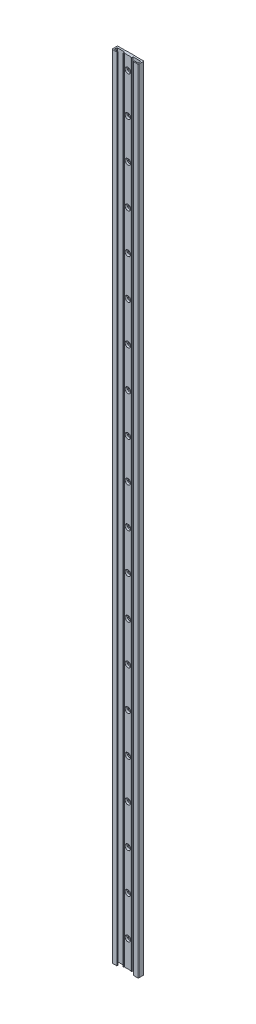
SolidWorks part; units mm, degrees
ref_plane "Front Plane" through (0, 0, 0) normal (0, 0, 1) x (1, 0, 0)
ref_plane "Top Plane" through (0, 0, 0) normal (0, 1, 0) x (1, 0, 0)
ref_plane "Right Plane" through (0, 0, 0) normal (1, 0, 0) x (0, 0, -1)
ref_plane "Plane4" through (0, 0, 8.7) normal (0, 0, 1) x (1, 0, 0)
sketch "Sketch1" plane through (0, 0, 8.7) normal (0, 0, 1) x (1, 0, 0)
  line L0 (-20, 0) -> (20, 0)
  line L1 (20, 0) -> (20, 1200)
  line L2 (20, 1200) -> (-20, 1200)
  line L3 (-20, 1200) -> (-20, 0)
  dimension "D1" = 1200
extrude "Boss-Extrude1" add sketch "Sketch1" against normal blind 8.7
sketch "Sketch2" plane through (0, 0, 0) normal (0, -1, 0) x (1, 0, 0)
  line L0 (12.5, 8.7) -> (-12.5, 8.7)
  line L1 (-12.5, 8.7) -> (-12.5, 7.2)
  line L2 (-12.5, 7.2) -> (-18, 7.2)
  line L3 (-18, 7.2) -> (-18, 2.8)
  line L4 (-18, 2.8) -> (-6.3, 2.8)
  line L5 (-6.3, 2.8) -> (-6.3, 5.5)
  line L6 (-6.3, 5.5) -> (-4.75, 5.5)
  line L7 (-4.75, 5.5) -> (-4.75, 4.5)
  line L8 (-4.75, 4.5) -> (4.75, 4.5)
  line L9 (4.75, 4.5) -> (4.75, 5.5)
  line L10 (4.75, 5.5) -> (6.3, 5.5)
  line L11 (6.3, 5.5) -> (6.3, 2.8)
  line L12 (6.3, 2.8) -> (18, 2.8)
  line L13 (18, 2.8) -> (18, 7.2)
  line L14 (18, 7.2) -> (12.5, 7.2)
  line L15 (12.5, 7.2) -> (12.5, 8.7)
extrude "Cut-Extrude1" cut sketch "Sketch2" against normal through all
sketch "Sketch3" plane through (0, 0, 0) normal (0, -1, 0) x (1, 0, 0)
  line L0 (8, 0.2) -> (8, 0)
  line L1 (8, 0) -> (20, 0)
  line L2 (20, 0) -> (20, 0.2)
  line L3 (20, 0.2) -> (8, 0.2)
extrude "Cut-Extrude2" cut sketch "Sketch3" against normal through all
sketch "Sketch4" plane through (0, 0, 0) normal (0, -1, 0) x (1, 0, 0)
  line L0 (-8, 0) -> (-8, 0.2)
  line L1 (-8, 0.2) -> (-20, 0.2)
  line L2 (-20, 0.2) -> (-20, 0)
  line L3 (-20, 0) -> (-8, 0)
extrude "Cut-Extrude3" cut sketch "Sketch4" against normal through all
draft "Draft1" type of draft neutral plane draft angle 45 faces to draft 2 face at (4.75, 600, 5) face at (-4.75, 600, 5) neutral plane through (-4.75, 1200, 4.5) neutral plane normal (0, 0, 1) parameters "D1"=45
hole_wizard "CBORE for M4 Hex Head Machine Screw1" positions "Sketch6" profile "Sketch5" counterbore size "M4" standard "ANSI Metric"
sketch "Sketch6" plane through (0, 0, 4.5) normal (0, 0, 1) x (1, 0, 0)
  point P0 (0, 160)
  point P1 (0, 100)
  point P2 (0, 40)
  point P12 (0, 220)
  point P13 (0, 280)
  point P14 (0, 340)
  point P15 (0, 400)
  point P16 (0, 460)
  point P17 (0, 520)
  point P18 (0, 580)
  point P19 (0, 640)
  point P20 (0, 700)
  point P21 (0, 760)
  point P22 (0, 820)
  point P23 (0, 880)
  point P24 (0, 940)
  point P25 (0, 1000)
  point P26 (0, 1060)
  point P27 (0, 1120)
  point P28 (0, 1180)
  dimension "D1" = 18
sketch "Sketch5" plane through (0, 160, 4.5) normal (1, 0, 0) x (0, -1, 0)
  line L0 (0, 0) -> (0, 4.5)
  line L1 (0, 4.5) -> (2.25, 4.5)
  line L3 (2.25, 4.5) -> (2.25, 3.1)
  line L4 (2.25, 3.1) -> (4.25, 3.1)
  line L5 (4.25, 3.1) -> (4.25, 0)
  line L7 (4.25, 0) -> (0, 0)
  line L11 (0, -6.35) -> (0, 107.95) construction
  dimension "Thru Hole Dia." = 4.5
  dimension "Thru Hole Depth" = 4.5
  dimension "C'Bore Dia." = 8.5
  dimension "C'Bore Depth" = 3.1
fillet "Fillet1" radius 0.5 6 edges at (-18, 600, 7.2) (-18, 600, 2.8) (-20, 600, 0.2) (18, 600, 7.2) (20, 600, 0.2) (18, 600, 2.8)
fillet "Fillet2" radius 1 2 edges at (20, 600, 8.7) (-20, 600, 8.7)
